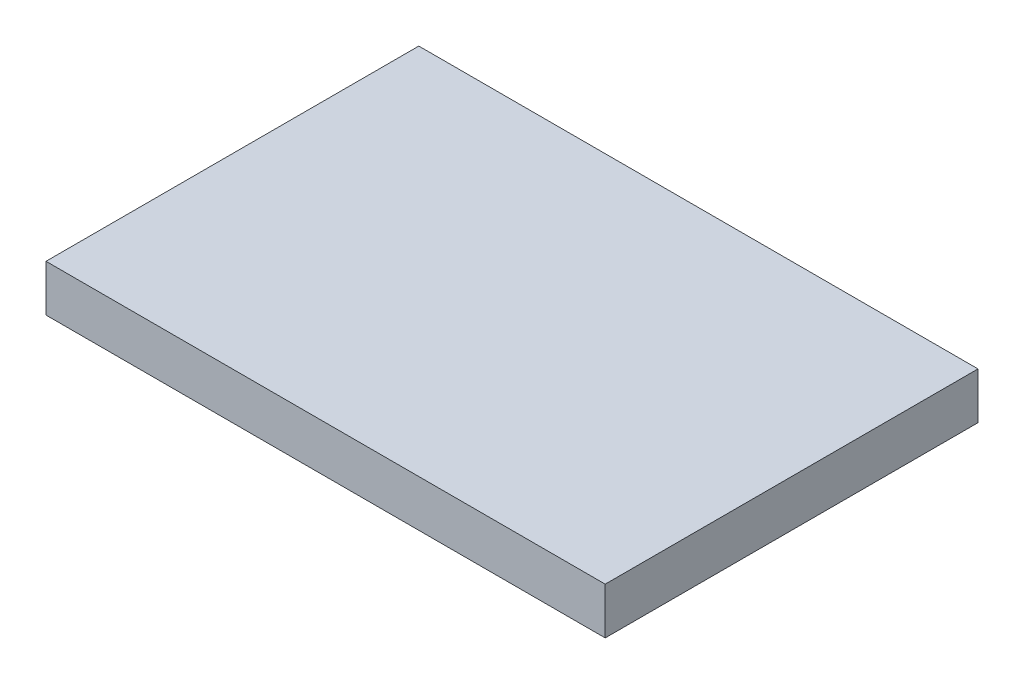
SolidWorks part; units mm, degrees
ref_plane "Front Plane" through (0, 0, 0) normal (0, 0, 1) x (1, 0, 0)
ref_plane "Top Plane" through (0, 0, 0) normal (0, 1, 0) x (1, 0, 0)
ref_plane "Right Plane" through (0, 0, 0) normal (1, 0, 0) x (0, 0, -1)
sketch "Sketch1" plane through (0, 340, 0) normal (0, -1, 0) x (1, 0, 0)
  line L1 (-86.4895, 26.9213) -> (33.5105, 26.9213)
  line L2 (-86.4895, 26.9213) -> (-86.4895, -53.0787)
  line L3 (-86.4895, -53.0787) -> (33.5105, -53.0787)
  line L4 (33.5105, 26.9213) -> (33.5105, -53.0787)
  dimension "D1" = 80
  dimension "D2" = 120
extrude "Boss-Extrude1" add sketch "Sketch1" along normal blind 10
